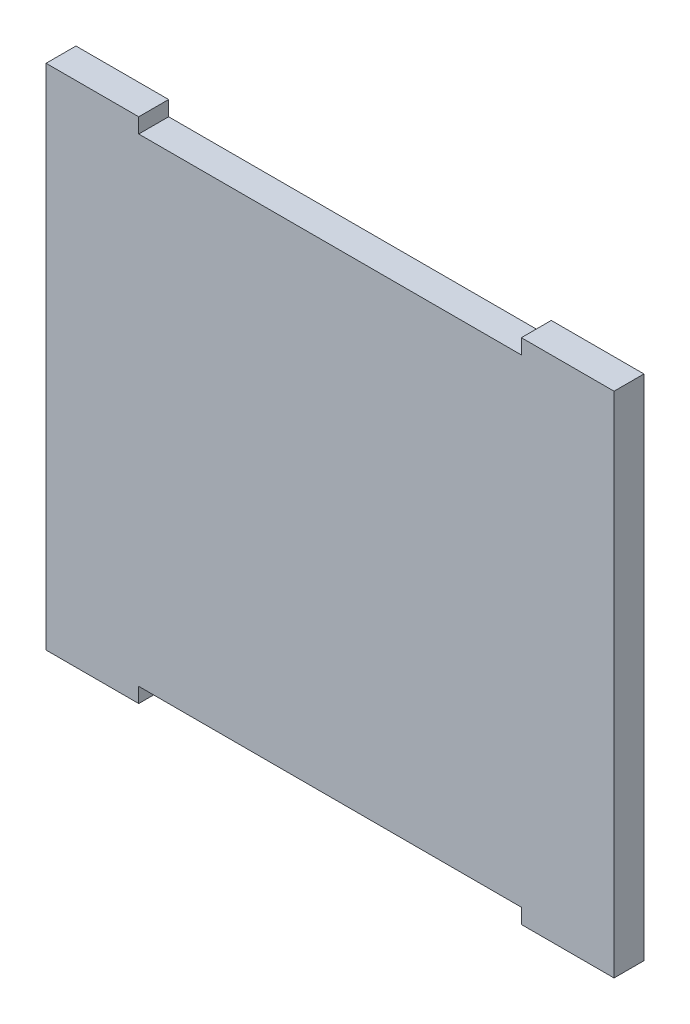
SolidWorks part; units mm, degrees
ref_plane "前视基准面" through (0, 0, 0) normal (0, 0, 1) x (1, 0, 0)
ref_plane "上视基准面" through (0, 0, 0) normal (0, 1, 0) x (1, 0, 0)
ref_plane "右视基准面" through (0, 0, 0) normal (1, 0, 0) x (0, 0, -1)
sketch "草图1" plane through (0, 0, 0) normal (0, 0, 1) x (1, 0, 0)
  line L0 (1270.8641, 538.563) -> (1398.8641, 538.563)
  line L1 (1429.8641, 543.563) -> (1429.8641, 373.563)
  line L2 (1398.8641, 378.563) -> (1270.8641, 378.563)
  line L3 (1239.8641, 373.563) -> (1239.8641, 543.563)
  line L4 (1398.8641, 538.563) -> (1398.8641, 543.563)
  line L5 (1398.8641, 543.563) -> (1429.8641, 543.563)
  line L6 (1270.8641, 538.563) -> (1270.8641, 543.563)
  line L7 (1270.8641, 543.563) -> (1239.8641, 543.563)
  line L8 (1270.8641, 378.563) -> (1398.8641, 378.563)
  line L9 (1398.8641, 378.563) -> (1398.8641, 373.563)
  line L10 (1398.8641, 373.563) -> (1429.8641, 373.563)
  line L11 (1270.8641, 378.563) -> (1270.8641, 373.563)
  line L12 (1270.8641, 373.563) -> (1239.8641, 373.563)
extrude "凸台-拉伸1" add sketch "草图1" along normal blind 10 contours L12 L11 L2 L9 L10 L1 L5 L4 L0 L6 L7 L3
